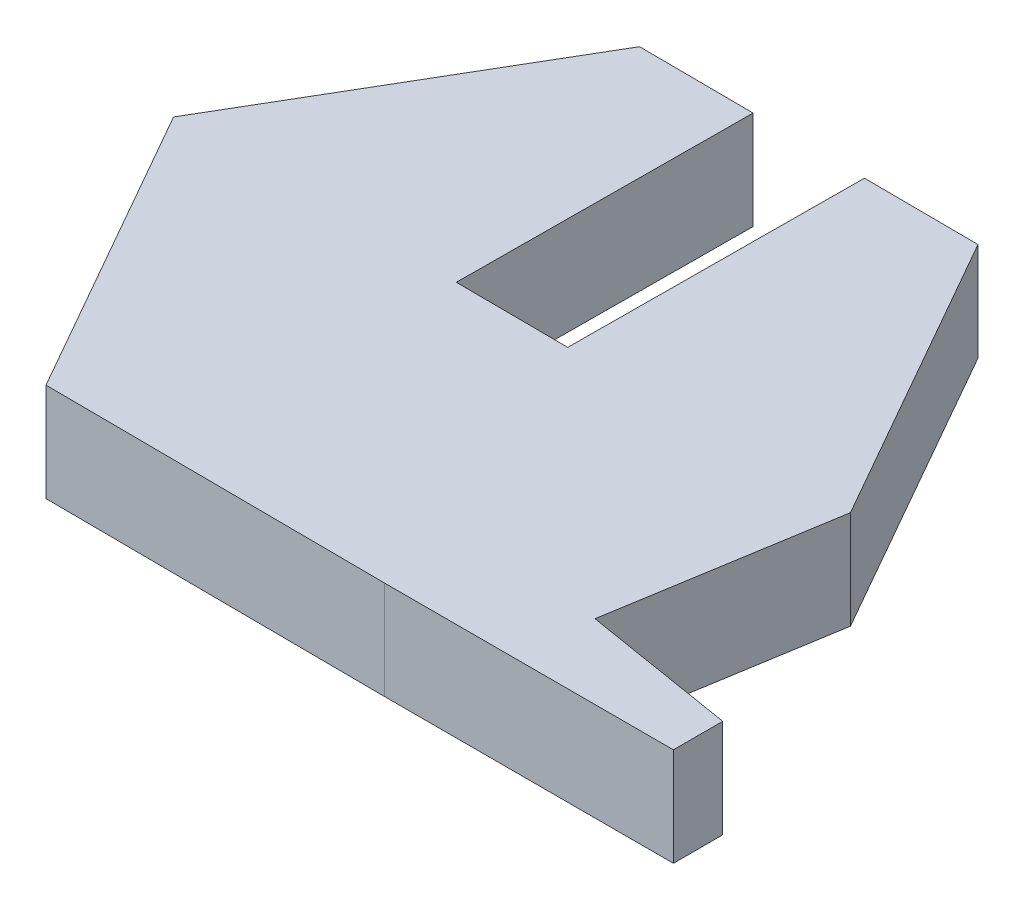
SolidWorks part; units mm, degrees
ref_plane "Front Plane" through (0, 0, 0) normal (0, 0, 1) x (1, 0, 0)
ref_plane "Top Plane" through (0, 0, 0) normal (0, 1, 0) x (1, 0, 0)
ref_plane "Right Plane" through (0, 0, 0) normal (1, 0, 0) x (0, 0, -1)
sketch "Sketch1" plane through (0, 0, 0) normal (0, 1, 0) x (1, 0, 0)
  line L10 (12.6941, -6.9341) -> (12.6941, -8.1889)
  line L12 (-3.314, -8.1347) -> (5.346, -8.1889)
  line L13 (12.6941, -8.1889) -> (5.346, -8.1889)
  line L14 (8.8103, -6.2992) -> (12.6941, -6.9341)
  line L15 (9.723, -0.7161) -> (5.4399, 6.8109)
  line L16 (-3.2202, 6.865) -> (-7.5972, -0.6077)
  line L17 (-7.5972, -0.6077) -> (-3.314, -8.1347)
  line L18 (9.723, -0.7161) -> (8.8103, -6.2992)
  line L19 (5.4399, 6.8109) -> (-3.2202, 6.865)
extrude "Boss-Extrude1" add sketch "Sketch1" along normal blind 2.5
sketch "Sketch2" plane through (0.0428, 0, -6.8446) normal (0.0063, 0, -1) x (-1, 0, -0.0063)
  line L0 (-5.3972, 0) -> (3.2631, 0) construction
  line L1 (-2.4922, 0) -> (0.3578, 0)
  line L2 (-2.4922, 0) -> (-2.4922, 2.5)
  line L3 (-2.4922, 2.5) -> (0.3578, 2.5)
  line L4 (0.3578, 0) -> (0.3578, 2.5)
  line L5 (-5.3972, 2.5) -> (3.2631, 2.5) construction
  line L6 (-5.3972, 2.5) -> (-5.3972, 0) construction
  dimension "D1" = 2.85
  dimension "D2" = 2.905
extrude "Cut-Extrude1" cut sketch "Sketch2" against normal blind 7.5
